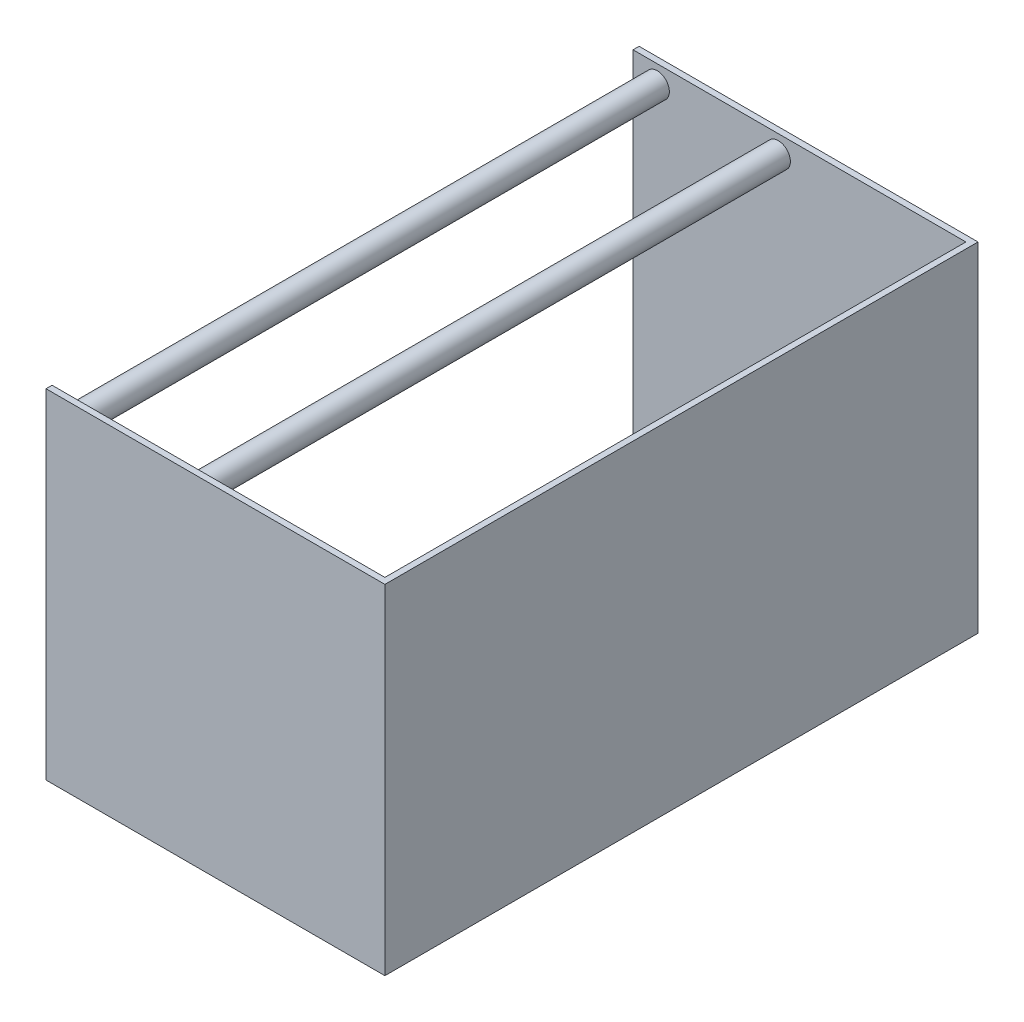
SolidWorks part; units mm, degrees
ref_plane "Front Plane" through (0, 0, 0) normal (0, 0, 1) x (1, 0, 0)
ref_plane "Top Plane" through (0, 0, 0) normal (0, 1, 0) x (1, 0, 0)
ref_plane "Right Plane" through (0, 0, 0) normal (1, 0, 0) x (0, 0, -1)
sketch "Sketch1" plane through (0, 0, 0) normal (0, 1, 0) x (1, 0, 0)
  line L1 (0, 0) -> (355.6, 0)
  line L2 (0, 0) -> (0, 622.3)
  line L3 (0, 622.3) -> (355.6, 622.3)
  line L4 (355.6, 0) -> (355.6, 622.3)
  dimension "D1" = 355.6
  dimension "D2" = 622.3
extrude "Boss-Extrude1" add sketch "Sketch1" along normal blind 355.6
shell "Shell1" thickness 6.35
sketch "Sketch2" plane through (0, 0, -622.3) normal (0, 0, -1) x (-1, 0, 0)
  line L0 (-355.6, 355.6) -> (0, 355.6) construction
  line L1 (-355.6, 355.6) -> (-355.6, 0) construction
  circle A0 centre (-152.4, 336.55) radius 12.7
  circle A1 centre (-25.4, 336.55) radius 12.7
  point P8 (-66.4194, 336.55)
  point P9 (0, 0)
  dimension "D1" = 25.4
  dimension "D2" = 19.05
  dimension "D3" = 203.2
  dimension "D4" = 127
extrude "Boss-Extrude2" add sketch "Sketch2" against normal up to surface (622.3 mm away) up to face at (177.8, 177.8, 0)
